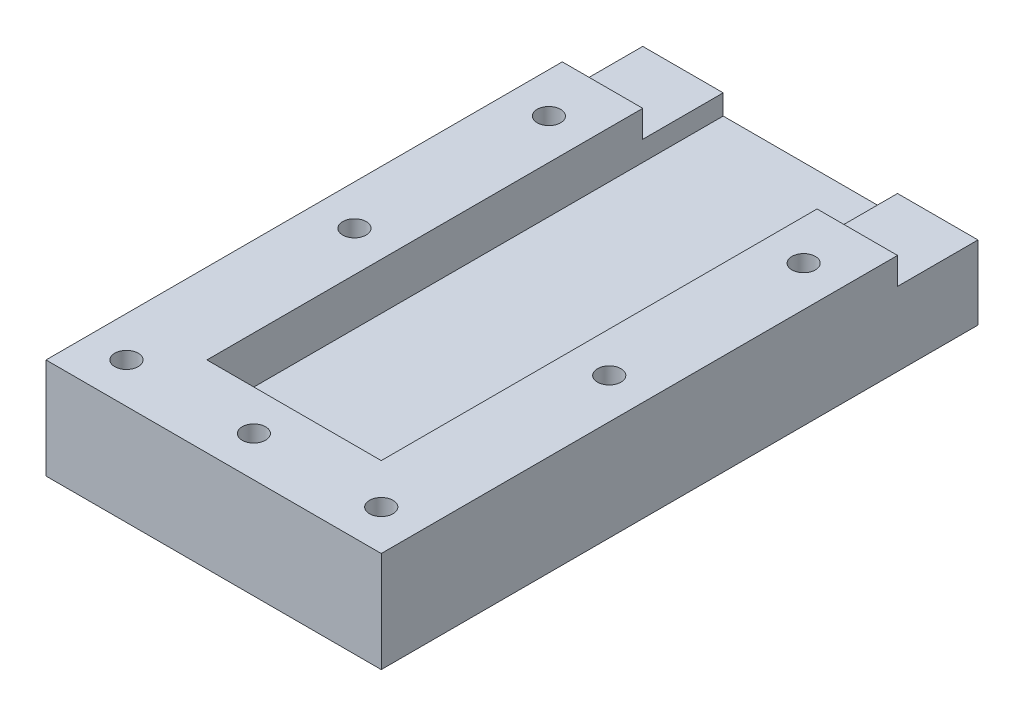
SolidWorks part; units mm, degrees
ref_plane "正面" through (0, 0, 0) normal (0, 0, 1) x (1, 0, 0)
ref_plane "平面" through (0, 0, 0) normal (0, 1, 0) x (1, 0, 0)
ref_plane "右側面" through (0, 0, 0) normal (1, 0, 0) x (0, 0, -1)
sketch "ｽｹｯﾁ1" plane through (0, 0, 0) normal (0, 0, 1) x (1, 0, 0)
  line L1 (-25, 15) -> (25, 15)
  line L2 (-25, 15) -> (-25, -15)
  line L3 (-25, -15) -> (25, -15)
  line L4 (25, 15) -> (25, -15)
  line L5 (-25, 15) -> (25, -15) construction
  line L6 (-25, -15) -> (25, 15) construction
  point P0 (0, 0)
  dimension "D1" = 30
  dimension "D2" = 50
extrude "ﾎﾞｽ - 押し出し1" add sketch "ｽｹｯﾁ1" along normal blind 89
sketch "ｽｹｯﾁ2" plane through (0, 0, 0) normal (0, 0, -1) x (-1, 0, 0)
  line L1 (13, 7) -> (-13, 7)
  line L2 (13, 7) -> (13, -7)
  line L3 (13, -7) -> (-13, -7)
  line L4 (-13, 7) -> (-13, -7)
  line L5 (13, 7) -> (-13, -7) construction
  line L6 (13, -7) -> (-13, 7) construction
  point P0 (0, 0)
  dimension "D1" = 26
  dimension "D2" = 14
extrude "ｶｯﾄ - 押し出し1" cut sketch "ｽｹｯﾁ2" against normal blind 77
ref_plane "平面1" through (0, 0, 0) normal (0, -1, 0) x (-1, 0, 0)
sketch "ｽｹｯﾁ5" plane through (13, 0, 0) normal (-1, 0, 0) x (0, 0, 1)
  line L0 (0, 7) -> (0, -7) construction
  line L1 (0, 4) -> (12, 4)
  line L2 (0, 4) -> (0, -4)
  line L3 (0, -4) -> (12, -4)
  line L4 (12, 4) -> (12, -4)
  line L6 (89, -15) -> (0, -15) construction
  dimension "D1" = 8
  dimension "D2" = 11
  dimension "D3" = 12
extrude "ｶｯﾄ - 押し出し4" cut sketch "ｽｹｯﾁ5" against normal through all
sketch "ｽｹｯﾁ6" plane through (-13, 0, 0) normal (1, 0, 0) x (0, 0, -1)
  line L0 (0, -7) -> (0, 7) construction
  line L1 (0, 4) -> (-12, 4)
  line L2 (0, 4) -> (0, -4)
  line L3 (0, -4) -> (-12, -4)
  line L4 (-12, 4) -> (-12, -4)
  line L5 (-89, -15) -> (0, -15) construction
  dimension "D1" = 12
  dimension "D2" = 8
  dimension "D3" = 11
extrude "ｶｯﾄ - 押し出し5" cut sketch "ｽｹｯﾁ6" against normal through all
sketch "ｽｹｯﾁ7" plane through (0, 15, 0) normal (0, 1, 0) x (1, 0, 0)
  line L0 (25, -89) -> (25, 0) construction
  line L1 (-25, -89) -> (-25, 0) construction
  line L2 (25, -89) -> (-25, -89) construction
  line L3 (25, 0) -> (-25, 0) construction
  circle A0 centre (19, -20) radius 1.75
  circle A1 centre (19, -49) radius 1.75
  circle A2 centre (19, -83) radius 1.75
  circle A3 centre (0, -83) radius 1.75
  circle A4 centre (-19, -83) radius 1.75
  circle A5 centre (-19, -49) radius 1.75
  circle A6 centre (-19, -20) radius 1.75
  dimension "D1" = 3.5
  dimension "D2" = 3.5
  dimension "D3" = 3.5
  dimension "D4" = 3.5
  dimension "D5" = 3.5
  dimension "D6" = 3.5
  dimension "D7" = 3.5
  dimension "D8" = 6
  dimension "D9" = 6
  dimension "D10" = 6
  dimension "D11" = 6
  dimension "D12" = 6
  dimension "D13" = 6
  dimension "D14" = 6
  dimension "D15" = 6
  dimension "D16" = 6
  dimension "D17" = 20
  dimension "D18" = 20
  dimension "D19" = 29
  dimension "D20" = 29
  dimension "D21" = 19
extrude "ｶｯﾄ - 押し出し6" cut sketch "ｽｹｯﾁ7" against normal through all
other "ｻｰﾌｪｽ ｶｯﾄ1"
